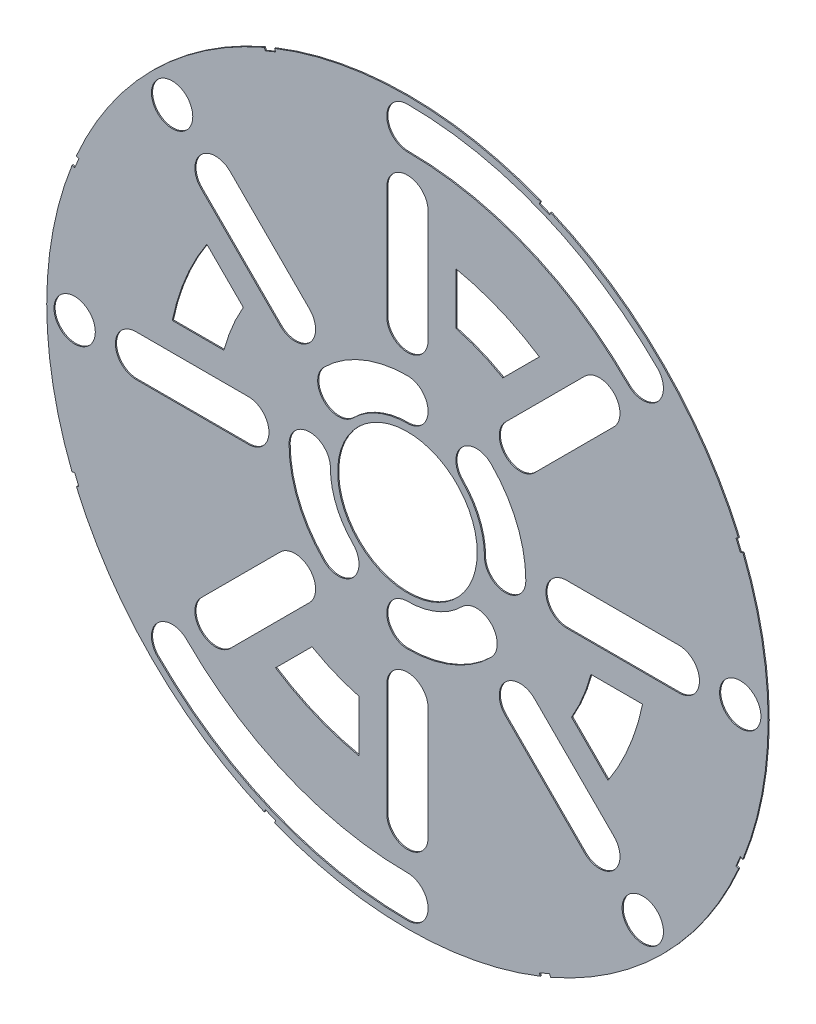
SolidWorks part; units mm, degrees
material "PTFE (general)"
ref_plane "Front Plane" through (0, 0, 0) normal (0, 0, 1) x (1, 0, 0)
ref_plane "Top Plane" through (0, 0, 0) normal (0, 1, 0) x (1, 0, 0)
ref_plane "Right Plane" through (0, 0, 0) normal (1, 0, 0) x (0, 0, -1)
sketch "Sketch4" plane through (0, 0, 0) normal (0, 0, 1) x (1, 0, 0)
  circle A0 centre (0, 0) radius 82.042
  dimension "D1" = 164.084
extrude "Boss-Extrude2" add sketch "Sketch4" along normal blind 0.254
sketch "Sketch5" plane through (0, 0, 0.254) normal (0, 0, 1) x (1, 0, 0)
  circle A0 centre (0, 0) radius 15.875
  dimension "D1" = 31.75
extrude "Cut-Extrude5" cut sketch "Sketch5" against normal through all
sketch "Sketch8" plane through (0, 0, 0.254) normal (0, 0, 1) x (1, 0, 0)
  line L2 (76.8696, 30.4658) -> (75.8976, 32.8124)
  line L3 (76.8696, 30.4658) -> (75.6963, 29.9798)
  line L4 (75.6963, 29.9798) -> (74.7243, 32.3264)
  line L5 (75.8976, 32.8124) -> (74.7243, 32.3264)
  line L6 (0, 0) -> (82.042, 0) construction
  line L7 (-30.4658, 76.8696) -> (-32.8124, 75.8976)
  line L8 (-30.4658, 76.8696) -> (-29.9798, 75.6963)
  line L9 (-32.8124, 75.8976) -> (-32.3264, 74.7243)
  line L10 (-29.9798, 75.6963) -> (-32.3264, 74.7243)
  line L11 (-32.8124, 75.8976) -> (-29.9798, 75.6963) construction
  line L12 (-30.4658, 76.8696) -> (-32.3264, 74.7243) construction
  line L13 (-75.8976, 32.8124) -> (-76.8696, 30.4658)
  line L14 (-75.8976, 32.8124) -> (-74.7243, 32.3264)
  line L15 (-74.7243, 32.3264) -> (-75.6963, 29.9798)
  line L16 (-76.8696, 30.4658) -> (-75.6963, 29.9798)
  line L17 (-75.8976, 32.8124) -> (-75.6963, 29.9798) construction
  line L18 (-76.8696, 30.4658) -> (-74.7243, 32.3264) construction
  line L19 (-76.8696, -30.4658) -> (-75.8976, -32.8124)
  line L20 (-76.8696, -30.4658) -> (-75.6963, -29.9798)
  line L21 (-75.6963, -29.9798) -> (-74.7243, -32.3264)
  line L22 (-75.8976, -32.8124) -> (-74.7243, -32.3264)
  line L23 (-76.8696, -30.4658) -> (-74.7243, -32.3264) construction
  line L24 (-75.8976, -32.8124) -> (-75.6963, -29.9798) construction
  line L25 (-32.8124, -75.8976) -> (-30.4658, -76.8696)
  line L26 (-32.8124, -75.8976) -> (-32.3264, -74.7243)
  line L27 (-32.3264, -74.7243) -> (-29.9798, -75.6963)
  line L28 (-30.4658, -76.8696) -> (-29.9798, -75.6963)
  line L29 (-32.8124, -75.8976) -> (-29.9798, -75.6963) construction
  line L30 (-30.4658, -76.8696) -> (-32.3264, -74.7243) construction
  line L31 (30.4658, -76.8696) -> (32.8124, -75.8976)
  line L32 (30.4658, -76.8696) -> (29.9798, -75.6963)
  line L33 (29.9798, -75.6963) -> (32.3264, -74.7243)
  line L34 (32.8124, -75.8976) -> (32.3264, -74.7243)
  line L35 (30.4658, -76.8696) -> (32.3264, -74.7243) construction
  line L36 (32.8124, -75.8976) -> (29.9798, -75.6963) construction
  line L37 (75.8976, -32.8124) -> (76.8696, -30.4658)
  line L38 (75.8976, -32.8124) -> (74.7243, -32.3264)
  line L39 (74.7243, -32.3264) -> (75.6963, -29.9798)
  line L40 (76.8696, -30.4658) -> (75.6963, -29.9798)
  line L41 (75.8976, -32.8124) -> (75.6963, -29.9798) construction
  line L42 (76.8696, -30.4658) -> (74.7243, -32.3264) construction
  line L43 (76.8696, 30.4658) -> (74.7243, 32.3264) construction
  line L44 (75.8976, 32.8124) -> (75.6963, 29.9798) construction
  line L45 (32.8124, 75.8976) -> (30.4658, 76.8696)
  line L46 (32.8124, 75.8976) -> (32.3264, 74.7243)
  line L47 (32.3264, 74.7243) -> (29.9798, 75.6963)
  line L48 (30.4658, 76.8696) -> (29.9798, 75.6963)
  line L49 (32.8124, 75.8976) -> (29.9798, 75.6963) construction
  line L50 (30.4658, 76.8696) -> (32.3264, 74.7243) construction
  circle A0 centre (0, 0) radius 82.042 construction
  point P3 (-31.3961, 75.7969)
  point P11 (-75.7969, 31.3961)
  point P15 (75.7969, 31.3961)
  point P20 (-75.7969, -31.3961)
  point P25 (-31.3961, -75.7969)
  point P26 (0, 0)
  point P31 (31.3961, -75.7969)
  point P36 (75.7969, -31.3961)
  point P45 (31.3961, 75.7969)
  point P46 (0, 0)
  dimension "D3" = 0.635
  dimension "D5" = 1.27
  dimension "D6" = 2.54
  dimension "D7" = 1.27
  dimension "D9" = 0.635
  dimension "D10" = 112.5
  dimension "D14" = 0.635
  dimension "D21" = 22.5
  dimension "D11" = 8
extrude "Cut-Extrude11" cut sketch "Sketch8" against normal through all
sketch "Sketch9" plane through (0, 0, 0.254) normal (0, 0, 1) x (1, 0, 0)
  line L0 (0, 0) -> (75.692, 0) construction
  line L1 (0, 0) -> (53.5223, 53.5223) construction
  line L2 (0, 0) -> (53.5223, -53.5223) construction
  circle A0 centre (22.225, 0) radius 4.699
  circle A1 centre (36.195, 0) radius 4.699
  circle A2 centre (61.722, 0) radius 4.699
  circle A3 centre (75.692, 0) radius 4.699
  circle A4 centre (0, 0) radius 15.875 construction
  circle A6 centre (15.7154, -15.7154) radius 4.699
  circle A7 centre (25.5937, -25.5937) radius 4.699
  circle A8 centre (43.644, -43.644) radius 4.699
  circle A9 centre (53.5223, -53.5223) radius 4.699
  circle A10 centre (0, -22.225) radius 4.699
  circle A11 centre (0, -36.195) radius 4.699
  circle A12 centre (0, -61.722) radius 4.699
  circle A13 centre (0, -75.692) radius 4.699
  circle A14 centre (-15.7154, -15.7154) radius 4.699
  circle A15 centre (-25.5937, -25.5937) radius 4.699
  circle A16 centre (-43.644, -43.644) radius 4.699
  circle A17 centre (-53.5223, -53.5223) radius 4.699
  circle A18 centre (-22.225, 0) radius 4.699
  circle A19 centre (-36.195, 0) radius 4.699
  circle A20 centre (-61.722, 0) radius 4.699
  circle A21 centre (-75.692, 0) radius 4.699
  circle A22 centre (-15.7154, 15.7154) radius 4.699
  circle A23 centre (-25.5937, 25.5937) radius 4.699
  circle A24 centre (-43.644, 43.644) radius 4.699
  circle A25 centre (-53.5223, 53.5223) radius 4.699
  circle A26 centre (0, 22.225) radius 4.699
  circle A27 centre (0, 36.195) radius 4.699
  circle A28 centre (0, 61.722) radius 4.699
  circle A29 centre (0, 75.692) radius 4.699
  circle A30 centre (15.7154, 15.7154) radius 4.699
  circle A31 centre (25.5937, 25.5937) radius 4.699
  circle A32 centre (43.644, 43.644) radius 4.699
  circle A33 centre (53.5223, 53.5223) radius 4.699
  point P74 (0, 0)
  dimension "D3" = 9.398
  dimension "D1" = 13.97
  dimension "D2" = 13.97
  dimension "D4" = 6.35
  dimension "D8" = 45
  dimension "D9" = 45
  dimension "D5" = 25.527
  dimension "D7" = 8
extrude "Cut-Extrude12" cut sketch "Sketch9" against normal through all
sketch "Sketch11" plane through (0, 0, 0.254) normal (0, 0, 1) x (1, 0, 0)
  line L0 (0, 0) -> (15.7154, 15.7154) construction
  line L1 (0, 0) -> (15.7154, -15.7154) construction
  line L2 (36.195, 0) -> (61.722, 0) construction
  line L3 (36.195, 4.699) -> (61.722, 4.699)
  line L4 (36.195, -4.699) -> (61.722, -4.699)
  line L5 (25.5937, -25.5937) -> (43.644, -43.644) construction
  line L6 (28.9164, -22.271) -> (46.9667, -40.3213)
  line L7 (22.271, -28.9164) -> (40.3213, -46.9667)
  line L8 (0, -36.195) -> (0, -61.722) construction
  line L9 (4.699, -36.195) -> (4.699, -61.722)
  line L10 (-4.699, -36.195) -> (-4.699, -61.722)
  line L11 (-25.5937, -25.5937) -> (-43.644, -43.644) construction
  line L12 (-22.271, -28.9164) -> (-40.3213, -46.9667)
  line L13 (-28.9164, -22.271) -> (-46.9667, -40.3213)
  line L14 (-36.195, 0) -> (-61.722, 0) construction
  line L15 (-36.195, -4.699) -> (-61.722, -4.699)
  line L16 (-36.195, 4.699) -> (-61.722, 4.699)
  line L17 (-25.5937, 25.5937) -> (-43.644, 43.644) construction
  line L18 (-28.9164, 22.271) -> (-46.9667, 40.3213)
  line L19 (-22.271, 28.9164) -> (-40.3213, 46.9667)
  line L20 (0, 36.195) -> (0, 61.722) construction
  line L21 (-4.699, 36.195) -> (-4.699, 61.722)
  line L22 (4.699, 36.195) -> (4.699, 61.722)
  line L23 (25.5937, 25.5937) -> (43.644, 43.644) construction
  line L24 (22.271, 28.9164) -> (40.3213, 46.9667)
  line L25 (28.9164, 22.271) -> (46.9667, 40.3213)
  line L26 (0, 0) -> (36.195, 0) construction
  line L27 (0, 0) -> (25.5937, -25.5937) construction
  line L28 (11.049, 41.7424) -> (11.049, 53.4806)
  line L29 (21.7035, 37.3292) -> (30.0037, 45.6293)
  line L30 (37.3292, -21.7035) -> (45.6293, -30.0037)
  line L31 (41.7424, -11.049) -> (53.4806, -11.049)
  line L32 (-21.7035, -37.3292) -> (-30.0037, -45.6293)
  line L33 (-11.049, -41.7424) -> (-11.049, -53.4806)
  line L34 (-37.3292, 21.7035) -> (-45.6293, 30.0037)
  line L35 (-41.7424, 11.049) -> (-53.4806, 11.049)
  arc A0 (15.7154, 15.7154) -> (22.225, 0) centre (0, 0) cw construction
  arc A1 (26.924, 0) -> (19.0381, 19.0381) centre (0, 0) ccw
  arc A2 (17.526, 0) -> (12.3928, 12.3928) centre (0, 0) ccw
  arc A3 (17.526, 0) -> (26.924, 0) centre (22.225, 0) ccw
  arc A4 (19.0381, 19.0381) -> (12.3928, 12.3928) centre (15.7154, 15.7154) ccw
  circle A5 centre (0, 75.692) radius 4.699 construction
  arc A6 (15.7154, -15.7154) -> (0, -22.225) centre (0, 0) cw construction
  circle A7 centre (22.225, 0) radius 4.699 construction
  arc A8 (0, -75.692) -> (-53.5223, -53.5223) centre (0, 0) cw construction
  arc A9 (0, -26.924) -> (19.0381, -19.0381) centre (0, 0) ccw
  arc A10 (0, -17.526) -> (12.3928, -12.3928) centre (0, 0) ccw
  arc A11 (0, -17.526) -> (0, -26.924) centre (0, -22.225) ccw
  arc A12 (19.0381, -19.0381) -> (12.3928, -12.3928) centre (15.7154, -15.7154) ccw
  arc A13 (-15.7154, -15.7154) -> (-22.225, 0) centre (0, 0) cw construction
  arc A14 (-26.924, 0) -> (-19.0381, -19.0381) centre (0, 0) ccw
  arc A15 (-17.526, 0) -> (-12.3928, -12.3928) centre (0, 0) ccw
  arc A16 (-17.526, 0) -> (-26.924, 0) centre (-22.225, 0) ccw
  arc A17 (-19.0381, -19.0381) -> (-12.3928, -12.3928) centre (-15.7154, -15.7154) ccw
  arc A18 (-15.7154, 15.7154) -> (0, 22.225) centre (0, 0) cw construction
  arc A19 (0, 26.924) -> (-19.0381, 19.0381) centre (0, 0) ccw
  arc A20 (0, 17.526) -> (-12.3928, 12.3928) centre (0, 0) ccw
  arc A21 (0, 17.526) -> (0, 26.924) centre (0, 22.225) ccw
  arc A22 (-19.0381, 19.0381) -> (-12.3928, 12.3928) centre (-15.7154, 15.7154) ccw
  arc A23 (53.5223, 53.5223) -> (0, 75.692) centre (0, 0) ccw construction
  arc A24 (56.845, 56.845) -> (0, 80.391) centre (0, 0) ccw
  arc A25 (50.1996, 50.1996) -> (0, 70.993) centre (0, 0) ccw
  arc A26 (50.1996, 50.1996) -> (56.845, 56.845) centre (53.5223, 53.5223) ccw
  arc A27 (0, 80.391) -> (0, 70.993) centre (0, 75.692) ccw
  circle A28 centre (53.5223, 53.5223) radius 4.699 construction
  arc A29 (-56.845, -56.845) -> (0, -80.391) centre (0, 0) ccw
  arc A30 (-50.1996, -50.1996) -> (0, -70.993) centre (0, 0) ccw
  arc A31 (-50.1996, -50.1996) -> (-56.845, -56.845) centre (-53.5223, -53.5223) ccw
  arc A32 (0, -80.391) -> (0, -70.993) centre (0, -75.692) ccw
  circle A33 centre (-53.5223, -53.5223) radius 4.699 construction
  arc A34 (21.7035, 37.3292) -> (11.049, 41.7424) centre (0, 0) ccw
  arc A35 (30.0037, 45.6293) -> (11.049, 53.4806) centre (0, 0) ccw
  arc A36 (36.195, 4.699) -> (36.195, -4.699) centre (36.195, 0) ccw
  arc A37 (61.722, -4.699) -> (61.722, 4.699) centre (61.722, 0) ccw
  arc A38 (28.9164, -22.271) -> (22.271, -28.9164) centre (25.5937, -25.5937) ccw
  arc A39 (40.3213, -46.9667) -> (46.9667, -40.3213) centre (43.644, -43.644) ccw
  arc A40 (4.699, -36.195) -> (-4.699, -36.195) centre (0, -36.195) ccw
  arc A41 (-4.699, -61.722) -> (4.699, -61.722) centre (0, -61.722) ccw
  arc A42 (-22.271, -28.9164) -> (-28.9164, -22.271) centre (-25.5937, -25.5937) ccw
  arc A43 (-46.9667, -40.3213) -> (-40.3213, -46.9667) centre (-43.644, -43.644) ccw
  arc A44 (-36.195, -4.699) -> (-36.195, 4.699) centre (-36.195, 0) ccw
  arc A45 (-61.722, 4.699) -> (-61.722, -4.699) centre (-61.722, 0) ccw
  arc A46 (-28.9164, 22.271) -> (-22.271, 28.9164) centre (-25.5937, 25.5937) ccw
  arc A47 (-40.3213, 46.9667) -> (-46.9667, 40.3213) centre (-43.644, 43.644) ccw
  arc A48 (-4.699, 36.195) -> (4.699, 36.195) centre (0, 36.195) ccw
  arc A49 (4.699, 61.722) -> (-4.699, 61.722) centre (0, 61.722) ccw
  arc A50 (22.271, 28.9164) -> (28.9164, 22.271) centre (25.5937, 25.5937) ccw
  arc A51 (46.9667, 40.3213) -> (40.3213, 46.9667) centre (43.644, 43.644) ccw
  arc A52 (37.3292, -21.7035) -> (41.7424, -11.049) centre (0, 0) ccw
  arc A53 (45.6293, -30.0037) -> (53.4806, -11.049) centre (0, 0) ccw
  arc A54 (-21.7035, -37.3292) -> (-11.049, -41.7424) centre (0, 0) ccw
  arc A55 (-30.0037, -45.6293) -> (-11.049, -53.4806) centre (0, 0) ccw
  arc A56 (-37.3292, 21.7035) -> (-41.7424, 11.049) centre (0, 0) ccw
  arc A57 (-45.6293, 30.0037) -> (-53.4806, 11.049) centre (0, 0) ccw
  point P5 (20.5332, 8.5051)
  point P16 (8.5051, -20.5332)
  point P23 (-20.5332, -8.5051)
  point P30 (-8.5051, 20.5332)
  point P39 (28.9661, 69.9303)
  point P53 (-28.9661, -69.9303)
  point P64 (48.9585, 0)
  point P74 (34.6189, -34.6189)
  point P81 (0, -48.9585)
  point P88 (-34.6189, -34.6189)
  point P95 (-48.9585, 0)
  point P102 (-34.6189, 34.6189)
  point P109 (0, 48.9585)
  point P116 (34.6189, 34.6189)
  point P140 (0, 0)
  dimension "D1" = 9.398
  dimension "D2" = 4
  dimension "D4" = 9.398
  dimension "D5" = 9.398
  dimension "D9" = 43.18
  dimension "D10" = 54.61
  dimension "D3" = 90
  dimension "D6" = 9.398
  dimension "D8" = 45
  dimension "D11" = 6.35
  dimension "D12" = 6.35
  dimension "D7" = 8
  dimension "D13" = 4
extrude "Cut-Extrude14" cut sketch "Sketch11" against normal through all
equation "\"CoilSep\"= 1.005"
equation "\"D5@Sketch9\"=\"CoilSep\""
